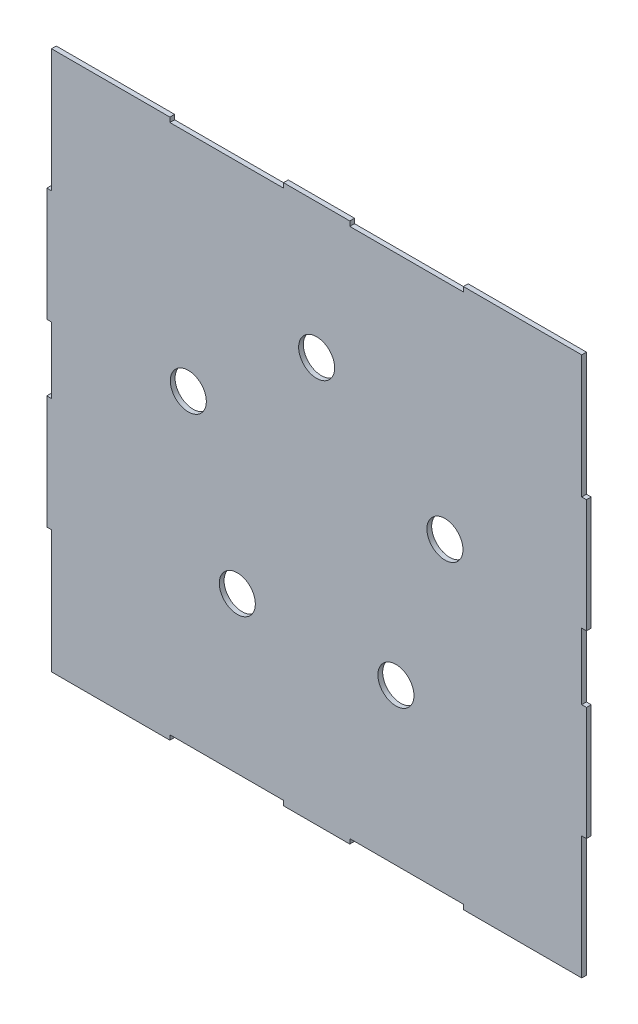
SolidWorks part; units mm, degrees
ref_plane "Front Plane" through (0, 0, 0) normal (0, 0, 1) x (1, 0, 0)
ref_plane "Top Plane" through (0, 0, 0) normal (0, 1, 0) x (1, 0, 0)
ref_plane "Right Plane" through (0, 0, 0) normal (1, 0, 0) x (0, 0, -1)
sketch "Sketch1" plane through (0, 0, 0) normal (0, 0, 1) x (1, 0, 0)
  line L1 (-180.975, -180.975) -> (180.975, -180.975)
  line L2 (-180.975, -180.975) -> (-180.975, 180.975)
  line L3 (-180.975, 180.975) -> (180.975, 180.975)
  line L4 (180.975, -180.975) -> (180.975, 180.975)
  line L5 (-180.975, -180.975) -> (180.975, 180.975) construction
  line L6 (-180.975, 180.975) -> (180.975, -180.975) construction
  point P0 (0, 0)
  dimension "D1" = 361.95
  dimension "D2" = 361.95
extrude "Boss-Extrude1" add sketch "Sketch1" along normal blind 3.175
sketch "Sketch2" plane through (0, 0, 3.175) normal (0, 0, 1) x (1, 0, 0)
  line L0 (180.975, 180.975) -> (-180.975, 180.975) construction
  line L2 (-98.425, 180.975) -> (-22.225, 180.975)
  line L3 (-98.425, 180.975) -> (-98.425, 177.8)
  line L4 (-98.425, 177.8) -> (-22.225, 177.8)
  line L5 (-22.225, 180.975) -> (-22.225, 177.8)
  line L7 (22.225, 180.975) -> (98.425, 180.975)
  line L8 (22.225, 180.975) -> (22.225, 177.8)
  line L9 (22.225, 177.8) -> (98.425, 177.8)
  line L10 (98.425, 180.975) -> (98.425, 177.8)
  line L15 (180.975, -180.975) -> (180.975, 180.975) construction
  line L16 (-180.975, 180.975) -> (-180.975, -180.975) construction
  line L17 (-258.7418, 0) -> (219.2412, 0) construction
  line L18 (98.425, -180.975) -> (98.425, -177.8)
  line L19 (22.225, -177.8) -> (98.425, -177.8)
  line L20 (22.225, -180.975) -> (22.225, -177.8)
  line L21 (22.225, -180.975) -> (98.425, -180.975)
  line L22 (-22.225, -180.975) -> (-22.225, -177.8)
  line L23 (-98.425, -177.8) -> (-22.225, -177.8)
  line L24 (-98.425, -180.975) -> (-98.425, -177.8)
  line L25 (-98.425, -180.975) -> (-22.225, -180.975)
  dimension "D1" = 76.2
  dimension "D2" = 76.2
  dimension "D3" = 82.55
  dimension "D4" = 82.55
  dimension "D5" = 44.45
  dimension "D6" = 3.175
extrude "Cut-Extrude1" cut sketch "Sketch2" against normal blind 3.175
sketch "Sketch3" plane through (0, 0, 3.175) normal (0, 0, 1) x (1, 0, 0)
  line L0 (-180.975, 180.975) -> (-180.975, -180.975) construction
  line L1 (-180.975, 180.975) -> (-177.8, 180.975)
  line L2 (-180.975, 180.975) -> (-180.975, 98.425)
  line L3 (-180.975, 98.425) -> (-177.8, 98.425)
  line L4 (-177.8, 180.975) -> (-177.8, 98.425)
  line L5 (-180.975, -22.225) -> (-177.8, -22.225)
  line L6 (-180.975, -22.225) -> (-180.975, 22.225)
  line L7 (-180.975, 22.225) -> (-177.8, 22.225)
  line L8 (-177.8, -22.225) -> (-177.8, 22.225)
  line L9 (-180.975, -180.975) -> (-98.425, -180.975) construction
  line L10 (-180.975, -98.425) -> (-177.8, -98.425)
  line L11 (-180.975, -98.425) -> (-180.975, -180.975)
  line L12 (-180.975, -180.975) -> (-177.8, -180.975)
  line L13 (-177.8, -98.425) -> (-177.8, -180.975)
  line L14 (0, 428.9604) -> (0, -247.9854) construction
  line L15 (177.8, -98.425) -> (177.8, -180.975)
  line L16 (180.975, -180.975) -> (177.8, -180.975)
  line L17 (180.975, -98.425) -> (180.975, -180.975)
  line L18 (180.975, -98.425) -> (177.8, -98.425)
  line L19 (177.8, -22.225) -> (177.8, 22.225)
  line L20 (180.975, 22.225) -> (177.8, 22.225)
  line L21 (180.975, -22.225) -> (180.975, 22.225)
  line L22 (180.975, -22.225) -> (177.8, -22.225)
  line L23 (177.8, 180.975) -> (177.8, 98.425)
  line L24 (180.975, 98.425) -> (177.8, 98.425)
  line L25 (180.975, 180.975) -> (180.975, 98.425)
  line L26 (180.975, 180.975) -> (177.8, 180.975)
  circle A0 centre (0, 0) radius 90.4875 construction
  circle A1 centre (0, 90.4875) radius 12.0777
  circle A2 centre (0, 0) radius 90.4875 construction
  circle A3 centre (86.0587, 27.9622) radius 12.0777
  circle A4 centre (0, 0) radius 90.4875 construction
  circle A5 centre (53.1872, -73.2059) radius 12.0777
  circle A6 centre (0, 0) radius 90.4875 construction
  circle A7 centre (-53.1872, -73.2059) radius 12.0777
  circle A8 centre (0, 0) radius 90.4875 construction
  circle A9 centre (-86.0587, 27.9622) radius 12.0777
  point P50 (0, 0)
  dimension "D8" = 180.975
  dimension "D9" = 24.1554
  dimension "D1" = 3.175
  dimension "D2" = 3.175
  dimension "D3" = 3.175
  dimension "D4" = 76.2
  dimension "D5" = 82.55
  dimension "D6" = 82.55
  dimension "D7" = 76.2
  dimension "D10" = 5
extrude "Cut-Extrude2" cut sketch "Sketch3" against normal blind 3.175
